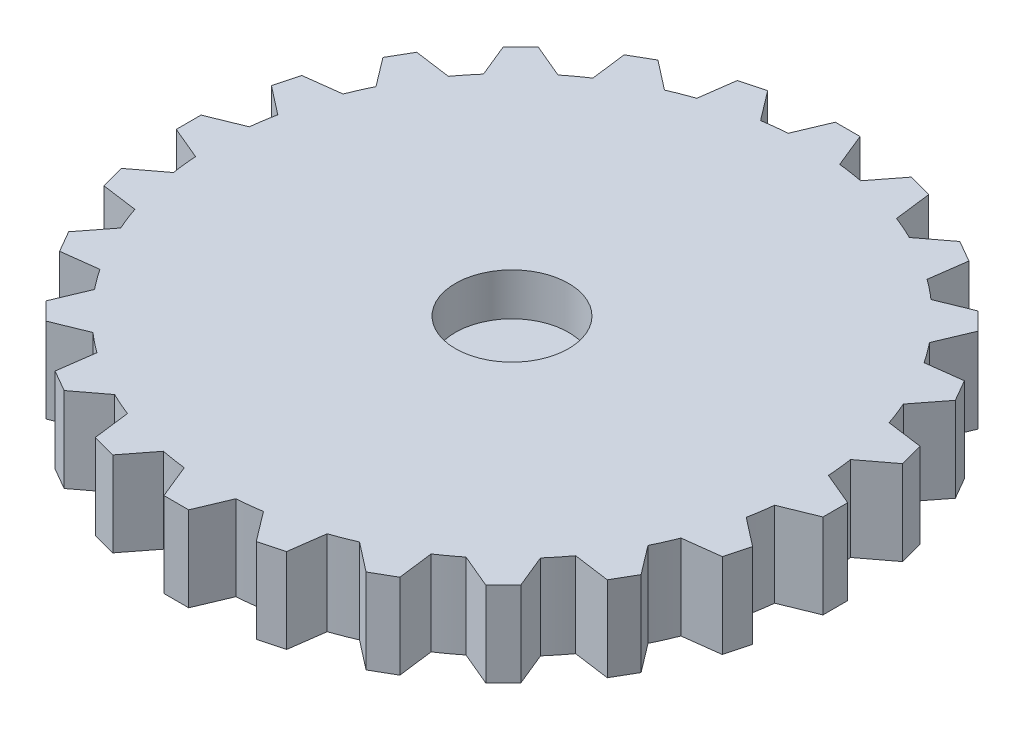
SolidWorks part; units mm, degrees
ref_plane "Front Plane" through (0, 0, 0) normal (0, 0, 1) x (1, 0, 0)
ref_plane "Top Plane" through (0, 0, 0) normal (0, 1, 0) x (1, 0, 0)
ref_plane "Right Plane" through (0, 0, 0) normal (1, 0, 0) x (0, 0, -1)
sketch "Sketch1" plane through (0, 0, 0) normal (0, 1, 0) x (1, 0, 0)
  line L111 (-0.5, 14.7462) -> (0.5, 14.7462)
  line L112 (0.5, 14.7462) -> (2, 12.5441)
  line L113 (-0.5, 14.7462) -> (-2, 12.5441)
  line L114 (6.433, 12.8885) -> (6.631, 10.2315)
  line L115 (5.567, 13.3885) -> (6.433, 12.8885)
  line L116 (5.567, 13.3885) -> (3.1669, 12.2315)
  line L117 (10.6423, 8.3132) -> (9.4853, 5.9131)
  line L118 (10.1423, 9.1792) -> (10.6423, 8.3132)
  line L119 (10.1423, 9.1792) -> (7.4853, 9.3772)
  line L120 (12, 2.2462) -> (9.798, 0.7462)
  line L121 (12, 3.2462) -> (12, 2.2462)
  line L122 (12, 3.2462) -> (9.798, 4.7462)
  line L123 (10.1423, -3.6868) -> (7.4853, -3.8849)
  line L124 (10.6423, -2.8208) -> (10.1423, -3.6868)
  line L125 (10.6423, -2.8208) -> (9.4853, -0.4208)
  line L126 (5.567, -7.8961) -> (3.1669, -6.7391)
  line L127 (6.433, -7.3961) -> (5.567, -7.8961)
  line L128 (6.433, -7.3961) -> (6.631, -4.7391)
  line L129 (-0.5, -9.2538) -> (-2, -7.0518)
  line L130 (0.5, -9.2538) -> (-0.5, -9.2538)
  line L131 (0.5, -9.2538) -> (2, -7.0518)
  line L132 (-6.433, -7.3961) -> (-6.631, -4.7391)
  line L133 (-5.567, -7.8961) -> (-6.433, -7.3961)
  line L134 (-5.567, -7.8961) -> (-3.1669, -6.7391)
  line L135 (-10.6423, -2.8208) -> (-9.4853, -0.4208)
  line L136 (-10.1423, -3.6868) -> (-10.6423, -2.8208)
  line L137 (-10.1423, -3.6868) -> (-7.4853, -3.8849)
  line L138 (-12, 3.2462) -> (-9.798, 4.7462)
  line L139 (-12, 2.2462) -> (-12, 3.2462)
  line L140 (-12, 2.2462) -> (-9.798, 0.7462)
  line L141 (-10.1423, 9.1792) -> (-7.4853, 9.3772)
  line L142 (-10.6423, 8.3132) -> (-10.1423, 9.1792)
  line L143 (-10.6423, 8.3132) -> (-9.4853, 5.9131)
  line L144 (-5.567, 13.3885) -> (-3.1669, 12.2315)
  line L145 (-6.433, 12.8885) -> (-5.567, 13.3885)
  line L146 (-6.433, 12.8885) -> (-6.631, 10.2315)
  arc A43 (-2, 12.5441) -> (-3.1669, 12.2315) centre (0, 2.7462) ccw
  arc A44 (-6.631, 10.2315) -> (-7.4853, 9.3772) centre (0, 2.7462) ccw
  arc A45 (-9.4853, 5.9131) -> (-9.798, 4.7462) centre (0, 2.7462) ccw
  arc A46 (-9.798, 0.7462) -> (-9.4853, -0.4208) centre (0, 2.7462) ccw
  arc A47 (-7.4853, -3.8849) -> (-6.631, -4.7391) centre (0, 2.7462) ccw
  arc A48 (-3.1669, -6.7391) -> (-2, -7.0518) centre (0, 2.7462) ccw
  arc A49 (2, -7.0518) -> (3.1669, -6.7391) centre (0, 2.7462) ccw
  arc A50 (6.631, -4.7391) -> (7.4853, -3.8849) centre (0, 2.7462) ccw
  arc A51 (9.4853, -0.4208) -> (9.798, 0.7462) centre (0, 2.7462) ccw
  arc A52 (9.798, 4.7462) -> (9.4853, 5.9131) centre (0, 2.7462) ccw
  arc A53 (7.4853, 9.3772) -> (6.631, 10.2315) centre (0, 2.7462) ccw
  arc A54 (3.1669, 12.2315) -> (2, 12.5441) centre (0, 2.7462) ccw
  point P6 (0, 0)
  point P8 (0, 0)
  point P9 (0, 0)
  point P12 (0, 2.7462)
  point P17 (0, 0)
  point P18 (0, 2.7462)
  point P22 (-2.5, 0.7462)
  point P63 (0, 0)
  point P68 (0, 0)
  point P69 (0, 2.7462)
  point P119 (0, 0)
  dimension "D1" = 20
  dimension "D8" = 12
sketch "Sketch2" plane through (0, 0, 0) normal (0, 1, 0) x (1, 0, 0)
  line L0 (-2, 0) -> (2, 0)
  line L1 (-23, -0.1) -> (-23, 0.1)
  line L2 (-21.1, 2) -> (-19.8997, 2)
  line L3 (-21.1, -2) -> (-19.8997, -2)
  line L4 (-20.6853, 4.6181) -> (-19.5438, 4.2472)
  line L5 (-19.4493, 8.4224) -> (-18.3078, 8.0515)
  line L6 (-21.9052, 7.0123) -> (-21.8434, 7.2025)
  line L7 (-18.2458, 10.7842) -> (-17.2748, 10.0787)
  line L8 (-15.8947, 14.0203) -> (-14.9237, 13.3148)
  line L9 (-18.6662, 13.4382) -> (-18.5486, 13.6)
  line L10 (-14.0203, 15.8947) -> (-13.3148, 14.9237)
  line L11 (-10.7842, 18.2458) -> (-10.0787, 17.2748)
  line L12 (-13.6, 18.5486) -> (-13.4382, 18.6662)
  line L13 (-8.4224, 19.4493) -> (-8.0515, 18.3078)
  line L14 (-4.6181, 20.6853) -> (-4.2472, 19.5438)
  line L15 (-7.2025, 21.8434) -> (-7.0123, 21.9052)
  line L16 (-2, 21.1) -> (-2, 19.8997)
  line L17 (2, 21.1) -> (2, 19.8997)
  line L18 (-0.1, 23) -> (0.1, 23)
  line L19 (4.6181, 20.6853) -> (4.2472, 19.5438)
  line L20 (8.4224, 19.4493) -> (8.0515, 18.3078)
  line L21 (7.0123, 21.9052) -> (7.2025, 21.8434)
  line L22 (10.7842, 18.2458) -> (10.0787, 17.2748)
  line L23 (14.0203, 15.8947) -> (13.3148, 14.9237)
  line L24 (13.4382, 18.6662) -> (13.6, 18.5486)
  line L25 (15.8947, 14.0203) -> (14.9237, 13.3148)
  line L26 (18.2458, 10.7842) -> (17.2748, 10.0787)
  line L27 (18.5486, 13.6) -> (18.6662, 13.4382)
  line L28 (19.4493, 8.4224) -> (18.3078, 8.0515)
  line L29 (20.6853, 4.6181) -> (19.5438, 4.2472)
  line L30 (21.8434, 7.2025) -> (21.9052, 7.0123)
  line L31 (21.1, 2) -> (19.8997, 2)
  line L32 (21.1, -2) -> (19.8997, -2)
  line L33 (23, 0.1) -> (23, -0.1)
  line L34 (20.6853, -4.6181) -> (19.5438, -4.2472)
  line L35 (19.4493, -8.4224) -> (18.3078, -8.0515)
  line L36 (21.9052, -7.0123) -> (21.8434, -7.2025)
  line L37 (18.2458, -10.7842) -> (17.2748, -10.0787)
  line L38 (15.8947, -14.0203) -> (14.9237, -13.3148)
  line L39 (18.6662, -13.4382) -> (18.5486, -13.6)
  line L40 (14.0203, -15.8947) -> (13.3148, -14.9237)
  line L41 (10.7842, -18.2458) -> (10.0787, -17.2748)
  line L42 (13.6, -18.5486) -> (13.4382, -18.6662)
  line L43 (8.4224, -19.4493) -> (8.0515, -18.3078)
  line L44 (4.6181, -20.6853) -> (4.2472, -19.5438)
  line L45 (7.2025, -21.8434) -> (7.0123, -21.9052)
  line L46 (2, -21.1) -> (2, -19.8997)
  line L47 (-2, -21.1) -> (-2, -19.8997)
  line L48 (0.1, -23) -> (-0.1, -23)
  line L49 (-4.6181, -20.6853) -> (-4.2472, -19.5438)
  line L50 (-8.4224, -19.4493) -> (-8.0515, -18.3078)
  line L51 (-7.0123, -21.9052) -> (-7.2025, -21.8434)
  line L52 (-10.7842, -18.2458) -> (-10.0787, -17.2748)
  line L53 (-14.0203, -15.8947) -> (-13.3148, -14.9237)
  line L54 (-13.4382, -18.6662) -> (-13.6, -18.5486)
  line L55 (-15.8947, -14.0203) -> (-14.9237, -13.3148)
  line L56 (-18.2458, -10.7842) -> (-17.2748, -10.0787)
  line L57 (-18.5486, -13.6) -> (-18.6662, -13.4382)
  line L58 (-19.4493, -8.4224) -> (-18.3078, -8.0515)
  line L59 (-20.6853, -4.6181) -> (-19.5438, -4.2472)
  line L60 (-21.8434, -7.2025) -> (-21.9052, -7.0123)
  arc A0 (-18.3078, -8.0515) -> (-17.2748, -10.0787) centre (0, 0) ccw
  arc A1 (-21.1, 2) -> (-23, 0.1) centre (-21.1, 0.1) ccw
  arc A2 (-21.1, -2) -> (-23, -0.1) centre (-21.1, -0.1) cw
  arc A3 (-20.6853, 4.6181) -> (-21.9052, 7.0123) centre (-20.0982, 6.4252) cw
  arc A4 (-19.4493, 8.4224) -> (-21.8434, 7.2025) centre (-20.0364, 6.6154) ccw
  arc A5 (-18.2458, 10.7842) -> (-18.6662, 13.4382) centre (-17.129, 12.3214) cw
  arc A6 (-15.8947, 14.0203) -> (-18.5486, 13.6) centre (-17.0115, 12.4832) ccw
  arc A7 (-14.0203, 15.8947) -> (-13.6, 18.5486) centre (-12.4832, 17.0115) cw
  arc A8 (-10.7842, 18.2458) -> (-13.4382, 18.6662) centre (-12.3214, 17.129) ccw
  arc A9 (-8.4224, 19.4493) -> (-7.2025, 21.8434) centre (-6.6154, 20.0364) cw
  arc A10 (-4.6181, 20.6853) -> (-7.0123, 21.9052) centre (-6.4252, 20.0982) ccw
  arc A11 (-2, 21.1) -> (-0.1, 23) centre (-0.1, 21.1) cw
  arc A12 (2, 21.1) -> (0.1, 23) centre (0.1, 21.1) ccw
  arc A13 (4.6181, 20.6853) -> (7.0123, 21.9052) centre (6.4252, 20.0982) cw
  arc A14 (8.4224, 19.4493) -> (7.2025, 21.8434) centre (6.6154, 20.0364) ccw
  arc A15 (10.7842, 18.2458) -> (13.4382, 18.6662) centre (12.3214, 17.129) cw
  arc A16 (14.0203, 15.8947) -> (13.6, 18.5486) centre (12.4832, 17.0115) ccw
  arc A17 (15.8947, 14.0203) -> (18.5486, 13.6) centre (17.0115, 12.4832) cw
  arc A18 (18.2458, 10.7842) -> (18.6662, 13.4382) centre (17.129, 12.3214) ccw
  arc A19 (19.4493, 8.4224) -> (21.8434, 7.2025) centre (20.0364, 6.6154) cw
  arc A20 (20.6853, 4.6181) -> (21.9052, 7.0123) centre (20.0982, 6.4252) ccw
  arc A21 (21.1, 2) -> (23, 0.1) centre (21.1, 0.1) cw
  arc A22 (21.1, -2) -> (23, -0.1) centre (21.1, -0.1) ccw
  arc A23 (20.6853, -4.6181) -> (21.9052, -7.0123) centre (20.0982, -6.4252) cw
  arc A24 (19.4493, -8.4224) -> (21.8434, -7.2025) centre (20.0364, -6.6154) ccw
  arc A25 (18.2458, -10.7842) -> (18.6662, -13.4382) centre (17.129, -12.3214) cw
  arc A26 (15.8947, -14.0203) -> (18.5486, -13.6) centre (17.0115, -12.4832) ccw
  arc A27 (14.0203, -15.8947) -> (13.6, -18.5486) centre (12.4832, -17.0115) cw
  arc A28 (10.7842, -18.2458) -> (13.4382, -18.6662) centre (12.3214, -17.129) ccw
  arc A29 (8.4224, -19.4493) -> (7.2025, -21.8434) centre (6.6154, -20.0364) cw
  arc A30 (4.6181, -20.6853) -> (7.0123, -21.9052) centre (6.4252, -20.0982) ccw
  arc A31 (2, -21.1) -> (0.1, -23) centre (0.1, -21.1) cw
  arc A32 (-2, -21.1) -> (-0.1, -23) centre (-0.1, -21.1) ccw
  arc A33 (-4.6181, -20.6853) -> (-7.0123, -21.9052) centre (-6.4252, -20.0982) cw
  arc A34 (-8.4224, -19.4493) -> (-7.2025, -21.8434) centre (-6.6154, -20.0364) ccw
  arc A35 (-10.7842, -18.2458) -> (-13.4382, -18.6662) centre (-12.3214, -17.129) cw
  arc A36 (-14.0203, -15.8947) -> (-13.6, -18.5486) centre (-12.4832, -17.0115) ccw
  arc A37 (-15.8947, -14.0203) -> (-18.5486, -13.6) centre (-17.0115, -12.4832) cw
  arc A38 (-18.2458, -10.7842) -> (-18.6662, -13.4382) centre (-17.129, -12.3214) ccw
  arc A39 (-19.4493, -8.4224) -> (-21.8434, -7.2025) centre (-20.0364, -6.6154) cw
  arc A40 (-20.6853, -4.6181) -> (-21.9052, -7.0123) centre (-20.0982, -6.4252) ccw
  arc A41 (-19.8997, -2) -> (-19.5438, -4.2472) centre (0, 0) ccw
  arc A42 (-19.5438, 4.2472) -> (-19.8997, 2) centre (0, 0) ccw
  arc A43 (-17.2748, 10.0787) -> (-18.3078, 8.0515) centre (0, 0) ccw
  arc A44 (-13.3148, 14.9237) -> (-14.9237, 13.3148) centre (0, 0) ccw
  arc A45 (-8.0515, 18.3078) -> (-10.0787, 17.2748) centre (0, 0) ccw
  arc A46 (-2, 19.8997) -> (-4.2472, 19.5438) centre (0, 0) ccw
  arc A47 (4.2472, 19.5438) -> (2, 19.8997) centre (0, 0) ccw
  arc A48 (10.0787, 17.2748) -> (8.0515, 18.3078) centre (0, 0) ccw
  arc A49 (14.9237, 13.3148) -> (13.3148, 14.9237) centre (0, 0) ccw
  arc A50 (18.3078, 8.0515) -> (17.2748, 10.0787) centre (0, 0) ccw
  arc A51 (19.8997, 2) -> (19.5438, 4.2472) centre (0, 0) ccw
  arc A52 (19.5438, -4.2472) -> (19.8997, -2) centre (0, 0) ccw
  arc A53 (17.2748, -10.0787) -> (18.3078, -8.0515) centre (0, 0) ccw
  arc A54 (13.3148, -14.9237) -> (14.9237, -13.3148) centre (0, 0) ccw
  arc A55 (8.0515, -18.3078) -> (10.0787, -17.2748) centre (0, 0) ccw
  arc A56 (2, -19.8997) -> (4.2472, -19.5438) centre (0, 0) ccw
  arc A57 (-10.0787, -17.2748) -> (-8.0515, -18.3078) centre (0, 0) ccw
  arc A58 (-4.2472, -19.5438) -> (-2, -19.8997) centre (0, 0) ccw
  arc A59 (-14.9237, -13.3148) -> (-13.3148, -14.9237) centre (0, 0) ccw
  point P6 (0, 0)
  point P10 (-23, 2)
  point P170 (0, 0)
  dimension "D1" = 40
  dimension "D4" = 1.9
  dimension "D5" = 20
sketch "Sketch3" plane through (0, 0, 0) normal (0, 1, 0) x (1, 0, 0)
  line L0 (20.6069, -4.0443) -> (20.351, -4.9991) construction
  line L1 (23.3015, -1.3115) -> (23.3015, 0.4385)
  line L2 (23.3015, 0.4385) -> (20.9515, 1.4269)
  line L3 (23.3015, -1.3115) -> (20.8737, -2.3)
  line L4 (22.621, -5.6073) -> (20.6069, -4.0443)
  line L5 (22.168, -7.2977) -> (22.621, -5.6073)
  line L6 (22.168, -7.2977) -> (19.5671, -7.6241)
  line L7 (20.3989, -11.271) -> (18.858, -9.24)
  line L8 (19.5239, -12.7866) -> (20.3989, -11.271)
  line L9 (19.5239, -12.7866) -> (16.9271, -12.4287)
  line L10 (16.7867, -16.1666) -> (15.8239, -13.8059)
  line L11 (15.5492, -17.404) -> (16.7867, -16.1666)
  line L12 (15.5492, -17.404) -> (13.1336, -16.3863)
  line L13 (12.0304, -19.9604) -> (11.7115, -17.431)
  line L14 (10.5149, -20.8354) -> (12.0304, -19.9604)
  line L15 (10.5149, -20.8354) -> (8.445, -19.2271)
  line L16 (6.4544, -22.394) -> (6.8009, -19.8682)
  line L17 (4.764, -22.8469) -> (6.4544, -22.394)
  line L18 (4.764, -22.8469) -> (3.1809, -20.7577)
  line L19 (0.4385, -23.3015) -> (1.4269, -20.9515)
  line L20 (-1.3115, -23.3015) -> (0.4385, -23.3015)
  line L21 (-1.3115, -23.3015) -> (-2.3, -20.8737)
  line L22 (-5.6073, -22.621) -> (-4.0443, -20.6069)
  line L23 (-7.2977, -22.168) -> (-5.6073, -22.621)
  line L24 (-7.2977, -22.168) -> (-7.6241, -19.5671)
  line L25 (-11.271, -20.3989) -> (-9.24, -18.858)
  line L26 (-12.7866, -19.5239) -> (-11.271, -20.3989)
  line L27 (-12.7866, -19.5239) -> (-12.4287, -16.9271)
  line L28 (-16.1666, -16.7867) -> (-13.8059, -15.8239)
  line L29 (-17.404, -15.5492) -> (-16.1666, -16.7867)
  line L30 (-17.404, -15.5492) -> (-16.3863, -13.1336)
  line L31 (-19.9604, -12.0304) -> (-17.431, -11.7115)
  line L32 (-20.8354, -10.5149) -> (-19.9604, -12.0304)
  line L33 (-20.8354, -10.5149) -> (-19.2271, -8.445)
  line L34 (-22.394, -6.4544) -> (-19.8682, -6.8009)
  line L35 (-22.8469, -4.764) -> (-22.394, -6.4544)
  line L36 (-22.8469, -4.764) -> (-20.7577, -3.1809)
  line L37 (-23.3015, -0.4385) -> (-20.9515, -1.4269)
  line L38 (-23.3015, 1.3115) -> (-23.3015, -0.4385)
  line L39 (-23.3015, 1.3115) -> (-20.8737, 2.3)
  line L40 (-22.621, 5.6073) -> (-20.6069, 4.0443)
  line L41 (-22.168, 7.2977) -> (-22.621, 5.6073)
  line L42 (-22.168, 7.2977) -> (-19.5671, 7.6241)
  line L43 (-20.3989, 11.271) -> (-18.858, 9.24)
  line L44 (-19.5239, 12.7866) -> (-20.3989, 11.271)
  line L45 (-19.5239, 12.7866) -> (-16.9271, 12.4287)
  line L46 (-16.7867, 16.1666) -> (-15.8239, 13.8059)
  line L47 (-15.5492, 17.404) -> (-16.7867, 16.1666)
  line L48 (-15.5492, 17.404) -> (-13.1336, 16.3863)
  line L49 (-12.0304, 19.9604) -> (-11.7115, 17.431)
  line L50 (-10.5149, 20.8354) -> (-12.0304, 19.9604)
  line L51 (-10.5149, 20.8354) -> (-8.445, 19.2271)
  line L52 (-6.4544, 22.394) -> (-6.8009, 19.8682)
  line L53 (-4.764, 22.8469) -> (-6.4544, 22.394)
  line L54 (-4.764, 22.8469) -> (-3.1809, 20.7577)
  line L55 (-0.4385, 23.3015) -> (-1.4269, 20.9515)
  line L56 (1.3115, 23.3015) -> (-0.4385, 23.3015)
  line L57 (1.3115, 23.3015) -> (2.3, 20.8737)
  line L58 (5.6073, 22.621) -> (4.0443, 20.6069)
  line L59 (7.2977, 22.168) -> (5.6073, 22.621)
  line L60 (7.2977, 22.168) -> (7.6241, 19.5671)
  line L61 (11.271, 20.3989) -> (9.24, 18.858)
  line L62 (12.7866, 19.5239) -> (11.271, 20.3989)
  line L63 (12.7866, 19.5239) -> (12.4287, 16.9271)
  line L64 (16.1666, 16.7867) -> (13.8059, 15.8239)
  line L65 (17.404, 15.5492) -> (16.1666, 16.7867)
  line L66 (17.404, 15.5492) -> (16.3863, 13.1336)
  line L67 (19.9604, 12.0304) -> (17.431, 11.7115)
  line L68 (20.8354, 10.5149) -> (19.9604, 12.0304)
  line L69 (20.8354, 10.5149) -> (19.2271, 8.445)
  line L70 (22.394, 6.4544) -> (19.8682, 6.8009)
  line L71 (22.8469, 4.764) -> (22.394, 6.4544)
  line L72 (22.8469, 4.764) -> (20.7577, 3.1809)
  line L73 (22.621, -5.6073) -> (20.351, -4.9991) construction
  line L74 (22.168, -7.2977) -> (19.823, -6.6694) construction
  line L75 (19.823, -6.6694) -> (19.5671, -7.6241) construction
  arc A0 (-9.24, -18.858) -> (-7.6241, -19.5671) centre (0, 0) ccw
  arc A1 (-13.8059, -15.8239) -> (-12.4287, -16.9271) centre (0, 0) ccw
  arc A2 (-17.431, -11.7115) -> (-16.3863, -13.1336) centre (0, 0) ccw
  arc A3 (-19.8682, -6.8009) -> (-19.2271, -8.445) centre (0, 0) ccw
  arc A4 (-20.9515, -1.4269) -> (-20.7577, -3.1809) centre (0, 0) ccw
  arc A5 (-20.6069, 4.0443) -> (-20.8737, 2.3) centre (0, 0) ccw
  arc A6 (-18.858, 9.24) -> (-19.5671, 7.6241) centre (0, 0) ccw
  arc A7 (-15.8239, 13.8059) -> (-16.9271, 12.4287) centre (0, 0) ccw
  arc A8 (13.8059, 15.8239) -> (12.4287, 16.9271) centre (0, 0) ccw
  arc A10 (13.8059, 15.8239) -> (12.4287, 16.9271) centre (0, 0) ccw
  arc A12 (9.24, 18.858) -> (7.6241, 19.5671) centre (0, 0) ccw
  arc A13 (13.8059, 15.8239) -> (12.4287, 16.9271) centre (0, 0) ccw
  arc A14 (17.431, 11.7115) -> (16.3863, 13.1336) centre (0, 0) ccw
  arc A15 (19.8682, 6.8009) -> (19.2271, 8.445) centre (0, 0) ccw
  arc A16 (20.9515, 1.4269) -> (20.7577, 3.1809) centre (0, 0) ccw
  arc A17 (20.6069, -4.0443) -> (20.8737, -2.3) centre (0, 0) ccw
  arc A18 (18.858, -9.24) -> (19.5671, -7.6241) centre (0, 0) ccw
  arc A19 (-4.0443, -20.6069) -> (-2.3, -20.8737) centre (0, 0) ccw
  arc A20 (1.4269, -20.9515) -> (3.1809, -20.7577) centre (0, 0) ccw
  arc A21 (6.8009, -19.8682) -> (8.445, -19.2271) centre (0, 0) ccw
  arc A22 (11.7115, -17.431) -> (13.1336, -16.3863) centre (0, 0) ccw
  arc A23 (15.8239, -13.8059) -> (16.9271, -12.4287) centre (0, 0) ccw
  arc A24 (-20.6069, 4.0443) -> (-20.8737, 2.3) centre (0, 0) ccw
  arc A25 (-20.6069, 4.0443) -> (-20.8737, 2.3) centre (0, 0) ccw
  arc A26 (-20.6069, 4.0443) -> (-20.8737, 2.3) centre (0, 0) ccw
  arc A27 (-18.858, 9.24) -> (-19.5671, 7.6241) centre (0, 0) ccw
  arc A28 (-18.858, 9.24) -> (-19.5671, 7.6241) centre (0, 0) ccw
  arc A29 (-18.858, 9.24) -> (-19.5671, 7.6241) centre (0, 0) ccw
  arc A30 (-15.8239, 13.8059) -> (-16.9271, 12.4287) centre (0, 0) ccw
  arc A31 (-15.8239, 13.8059) -> (-16.9271, 12.4287) centre (0, 0) ccw
  arc A32 (-15.8239, 13.8059) -> (-16.9271, 12.4287) centre (0, 0) ccw
  arc A33 (-11.7115, 17.431) -> (-13.1336, 16.3863) centre (0, 0) ccw
  arc A34 (-11.7115, 17.431) -> (-13.1336, 16.3863) centre (0, 0) ccw
  arc A35 (-11.7115, 17.431) -> (-13.1336, 16.3863) centre (0, 0) ccw
  arc A36 (-11.7115, 17.431) -> (-13.1336, 16.3863) centre (0, 0) ccw
  arc A37 (-6.8009, 19.8682) -> (-8.445, 19.2271) centre (0, 0) ccw
  arc A38 (-6.8009, 19.8682) -> (-8.445, 19.2271) centre (0, 0) ccw
  arc A39 (-6.8009, 19.8682) -> (-8.445, 19.2271) centre (0, 0) ccw
  arc A40 (-6.8009, 19.8682) -> (-8.445, 19.2271) centre (0, 0) ccw
  arc A41 (-1.4269, 20.9515) -> (-3.1809, 20.7577) centre (0, 0) ccw
  arc A42 (-1.4269, 20.9515) -> (-3.1809, 20.7577) centre (0, 0) ccw
  arc A43 (-1.4269, 20.9515) -> (-3.1809, 20.7577) centre (0, 0) ccw
  arc A44 (-1.4269, 20.9515) -> (-3.1809, 20.7577) centre (0, 0) ccw
  arc A45 (4.0443, 20.6069) -> (2.3, 20.8737) centre (0, 0) ccw
  arc A46 (4.0443, 20.6069) -> (2.3, 20.8737) centre (0, 0) ccw
  arc A47 (4.0443, 20.6069) -> (2.3, 20.8737) centre (0, 0) ccw
  arc A48 (4.0443, 20.6069) -> (2.3, 20.8737) centre (0, 0) ccw
  arc A49 (9.24, 18.858) -> (7.6241, 19.5671) centre (0, 0) ccw
  arc A50 (9.24, 18.858) -> (7.6241, 19.5671) centre (0, 0) ccw
  arc A51 (9.24, 18.858) -> (7.6241, 19.5671) centre (0, 0) ccw
  arc A52 (13.8059, 15.8239) -> (12.4287, 16.9271) centre (0, 0) ccw
  arc A53 (17.431, 11.7115) -> (16.3863, 13.1336) centre (0, 0) ccw
  arc A54 (19.8682, 6.8009) -> (19.2271, 8.445) centre (0, 0) ccw
  arc A55 (20.9515, 1.4269) -> (20.7577, 3.1809) centre (0, 0) ccw
  arc A56 (20.9515, 1.4269) -> (20.7577, 3.1809) centre (0, 0) ccw
  arc A57 (20.9515, 1.4269) -> (20.7577, 3.1809) centre (0, 0) ccw
  arc A58 (20.6069, -4.0443) -> (20.8737, -2.3) centre (0, 0) ccw
  arc A59 (20.6069, -4.0443) -> (20.8737, -2.3) centre (0, 0) ccw
  arc A60 (20.6069, -4.0443) -> (20.8737, -2.3) centre (0, 0) ccw
  arc A61 (18.858, -9.24) -> (19.5671, -7.6241) centre (0, 0) ccw
  arc A62 (18.858, -9.24) -> (19.5671, -7.6241) centre (0, 0) ccw
  arc A63 (18.858, -9.24) -> (19.5671, -7.6241) centre (0, 0) ccw
  arc A64 (15.8239, -13.8059) -> (16.9271, -12.4287) centre (0, 0) ccw
  arc A65 (15.8239, -13.8059) -> (16.9271, -12.4287) centre (0, 0) ccw
  arc A66 (15.8239, -13.8059) -> (16.9271, -12.4287) centre (0, 0) ccw
  arc A67 (11.7115, -17.431) -> (13.1336, -16.3863) centre (0, 0) ccw
  arc A68 (11.7115, -17.431) -> (13.1336, -16.3863) centre (0, 0) ccw
  arc A69 (11.7115, -17.431) -> (13.1336, -16.3863) centre (0, 0) ccw
  arc A70 (6.8009, -19.8682) -> (8.445, -19.2271) centre (0, 0) ccw
  arc A71 (6.8009, -19.8682) -> (8.445, -19.2271) centre (0, 0) ccw
  arc A72 (6.8009, -19.8682) -> (8.445, -19.2271) centre (0, 0) ccw
  arc A73 (1.4269, -20.9515) -> (3.1809, -20.7577) centre (0, 0) ccw
  arc A74 (1.4269, -20.9515) -> (3.1809, -20.7577) centre (0, 0) ccw
  arc A75 (1.4269, -20.9515) -> (3.1809, -20.7577) centre (0, 0) ccw
  arc A76 (-4.0443, -20.6069) -> (-2.3, -20.8737) centre (0, 0) ccw
  arc A77 (-4.0443, -20.6069) -> (-2.3, -20.8737) centre (0, 0) ccw
  arc A78 (-4.0443, -20.6069) -> (-2.3, -20.8737) centre (0, 0) ccw
  arc A79 (-9.24, -18.858) -> (-7.6241, -19.5671) centre (0, 0) ccw
  arc A80 (-9.24, -18.858) -> (-7.6241, -19.5671) centre (0, 0) ccw
  arc A81 (-9.24, -18.858) -> (-7.6241, -19.5671) centre (0, 0) ccw
  arc A82 (-13.8059, -15.8239) -> (-12.4287, -16.9271) centre (0, 0) ccw
  arc A83 (-13.8059, -15.8239) -> (-12.4287, -16.9271) centre (0, 0) ccw
  arc A84 (-13.8059, -15.8239) -> (-12.4287, -16.9271) centre (0, 0) ccw
  arc A85 (-17.431, -11.7115) -> (-16.3863, -13.1336) centre (0, 0) ccw
  arc A86 (-17.431, -11.7115) -> (-16.3863, -13.1336) centre (0, 0) ccw
  arc A87 (-17.431, -11.7115) -> (-16.3863, -13.1336) centre (0, 0) ccw
  arc A88 (-19.8682, -6.8009) -> (-19.2271, -8.445) centre (0, 0) ccw
  arc A89 (-19.8682, -6.8009) -> (-19.2271, -8.445) centre (0, 0) ccw
  arc A90 (-19.8682, -6.8009) -> (-19.2271, -8.445) centre (0, 0) ccw
  arc A91 (-20.9515, -1.4269) -> (-20.7577, -3.1809) centre (0, 0) ccw
  arc A92 (-20.9515, -1.4269) -> (-20.7577, -3.1809) centre (0, 0) ccw
  arc A93 (-20.9515, -1.4269) -> (-20.7577, -3.1809) centre (0, 0) ccw
  point P6 (0, 0)
  point P7 (0, -12.952)
  point P8 (-6.2727, 0)
  point P9 (11.4668, 0)
  point P10 (0, 0)
  point P108 (0, 0)
  dimension "D1" = 42
  dimension "D4" = 24
  dimension "1." = 1.75
  dimension "2.5" = 2.35
extrude "Boss-Extrude5" add sketch "Sketch3" along normal blind 6 separate body
extrude "Boss-Extrude6" add sketch "Sketch1" along normal blind 3 separate body
sketch "Sketch4" plane through (0, 6, 0) normal (0, 1, 0) x (1, 0, 0)
  circle A0 centre (0, 0) radius 4
  dimension "D1" = 8
extrude "Cut-Extrude1" cut sketch "Sketch4" against normal blind 10
sketch "Sketch5" plane through (0, 6, 0) normal (0, 1, 0) x (1, 0, 0)
  line L0 (-14.4568, -4) -> (14.4568, -4) construction
  circle A0 centre (-14.4568, -4) radius 1.5
  circle A1 centre (0, 0) radius 4 construction
  circle A2 centre (14.4568, -4) radius 1.5
  dimension "D1" = 3
  dimension "D2" = 15
  dimension "D3" = 3
  dimension "D4" = 15
extrude "Cut-Extrude2" [suppressed] cut sketch "Sketch5" against normal through all
